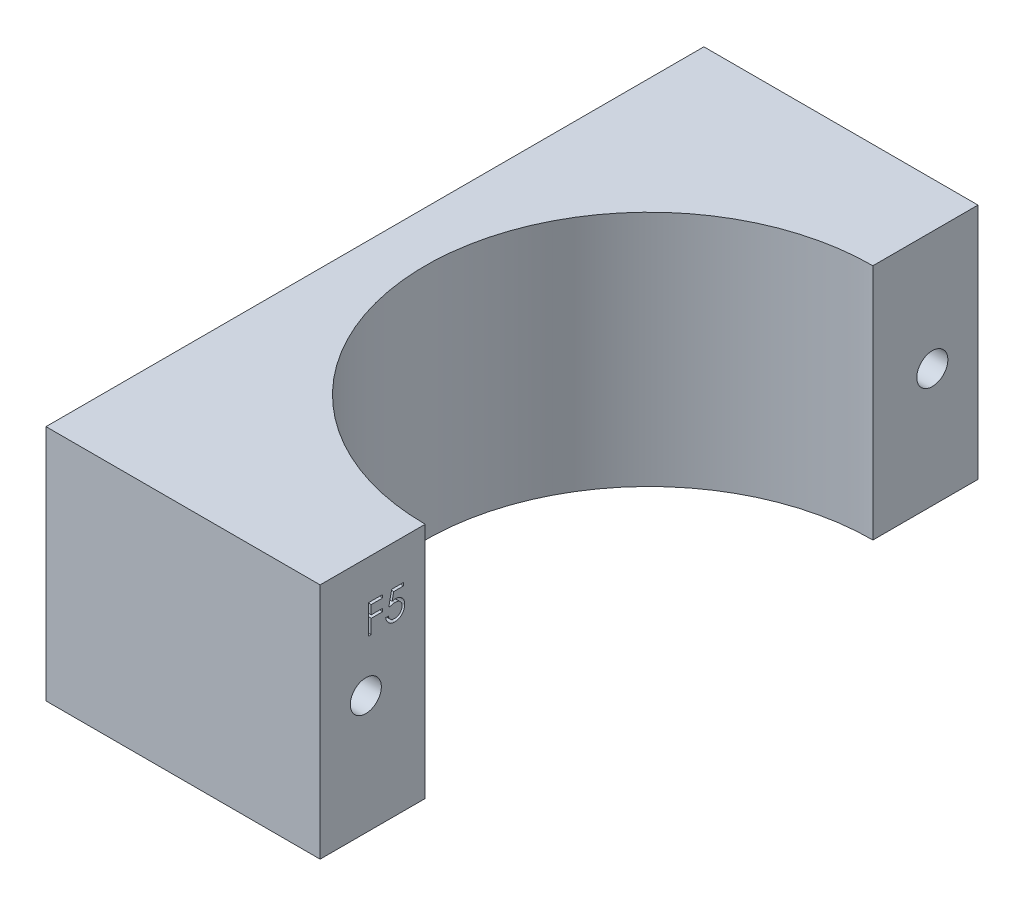
SolidWorks part; units mm, degrees
ref_plane "Front Plane" through (0, 0, 0) normal (0, 0, 1) x (1, 0, 0)
ref_plane "Top Plane" through (0, 0, 0) normal (0, 1, 0) x (1, 0, 0)
ref_plane "Right Plane" through (0, 0, 0) normal (1, 0, 0) x (0, 0, -1)
sketch "Sketch1" plane through (0, 0, 0) normal (0, 1, 0) x (1, 0, 0)
  line L0 (-46.9983, 32.5286) -> (-46.9983, -39.4714)
  line L1 (-46.9983, -39.4714) -> (-16.9983, -39.4714)
  line L2 (-16.9983, -39.4714) -> (-16.9983, -27.9714)
  line L3 (-46.9983, 32.5286) -> (-16.9983, 32.5286)
  line L4 (-16.9983, 32.5286) -> (-16.9983, 21.0286)
  arc A0 (-16.9983, 21.0286) -> (-16.9983, -27.9714) centre (-16.9983, -3.4714) ccw
  dimension "D1" = 72
  dimension "D2" = 30
  dimension "D3" = 30
  dimension "D4" = 11.5
  dimension "D5" = 11.5
extrude "Boss-Extrude1" add sketch "Sketch1" along normal blind 26
sketch "Sketch2" plane through (-16.9983, 0, 0) normal (1, 0, 0) x (0, 0, -1)
  line L0 (-34.4714, 26) -> (-34.4714, 0) construction
  line L1 (-39.4714, 26) -> (-27.9714, 26) construction
  line L2 (-39.4714, 0) -> (-27.9714, 0) construction
  line L3 (27.5286, 26) -> (27.5286, 0) construction
  line L4 (21.0286, 26) -> (32.5286, 26) construction
  line L5 (21.0286, 0) -> (32.5286, 0) construction
  line L6 (-39.4714, 26) -> (-39.4714, 0) construction
  line L7 (32.5286, 26) -> (32.5286, 0) construction
  circle A0 centre (-34.4714, 13) radius 1.7
  circle A1 centre (27.5286, 13) radius 1.7
  dimension "D1" = 5
  dimension "D2" = 5
extrude "Cut-Extrude1" cut sketch "Sketch2" against normal through all
sketch "Sketch3" plane through (-16.9983, 0, 0) normal (1, 0, 0) x (0, 0, -1)
  text T0 "F5"
extrude "Cut-Extrude2" cut sketch "Sketch3" against normal blind 1
